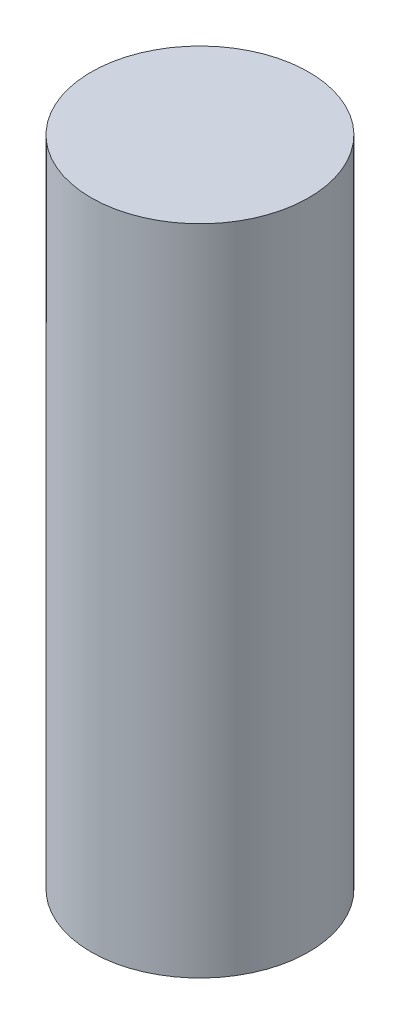
SolidWorks part; units mm, degrees
ref_plane "Front Plane" through (0, 0, 0) normal (0, 0, 1) x (1, 0, 0)
ref_plane "Top Plane" through (0, 0, 0) normal (0, 1, 0) x (1, 0, 0)
ref_plane "Right Plane" through (0, 0, 0) normal (1, 0, 0) x (0, 0, -1)
sketch "Sketch1" plane through (0, 0, 0) normal (0, 1, 0) x (1, 0, 0)
  circle A0 centre (0, 0) radius 2.5
extrude "Boss-Extrude1" add sketch "Sketch1" along normal blind 15
